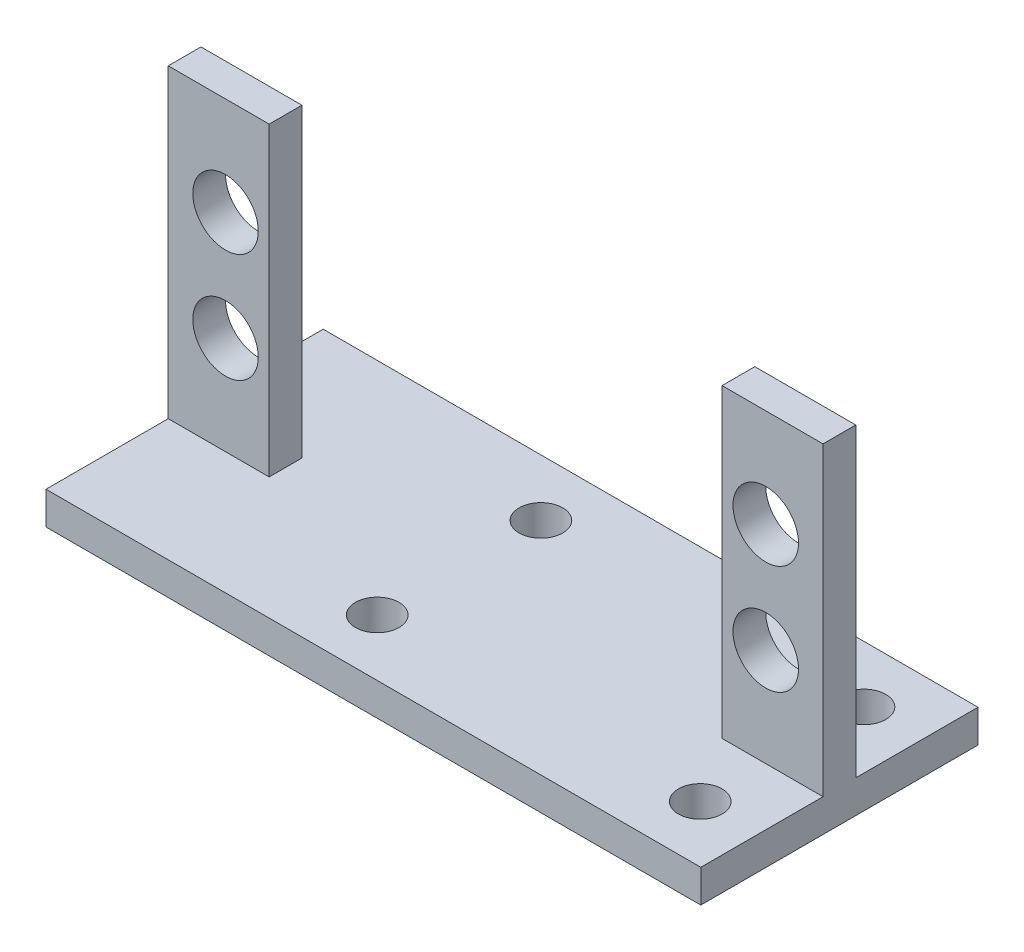
SolidWorks part; units mm, degrees
material "ABS"
ref_plane "Front" through (0, 0, 0) normal (0, 0, 1) x (1, 0, 0)
ref_plane "Top" through (0, 0, 0) normal (0, 1, 0) x (1, 0, 0)
ref_plane "Right" through (0, 0, 0) normal (1, 0, 0) x (0, 0, -1)
sketch "草图1" plane through (0, 0, 0) normal (0, 1, 0) x (1, 0, 0)
  line L0 (0, 0) -> (0, 12.7) construction
  line L1 (0, 0) -> (0, -12.7) construction
  line L2 (0, 0) -> (29, 0) construction
  line L3 (-29, 12.7) -> (29, 12.7)
  line L4 (29, 12.7) -> (29, -12.7)
  line L5 (-29, 12.7) -> (-29, -12.7)
  line L6 (-29, -12.7) -> (29, -12.7)
  point P10 (-29, 0)
extrude "凸台-拉伸1" add sketch "草图1" along normal blind 3
sketch "草图2" plane through (0, 3, 0) normal (0, 1, 0) x (1, 0, 0)
  line L0 (0, 12.7) -> (24.75, 12.7) construction
  line L1 (29, 12.7) -> (-29, 12.7) construction
  line L2 (0, 12.7) -> (-24.75, 12.7) construction
  line L3 (-24.75, 12.7) -> (-24.75, 9.7) construction
  line L4 (-24.75, 9.7) -> (-28.75, 9.7) construction
  line L5 (-24.75, 9.7) -> (-20.75, 9.7) construction
  line L6 (24.75, 12.7) -> (24.75, 9.7) construction
  line L7 (24.75, 9.7) -> (28.75, 9.7) construction
  line L8 (24.75, 9.7) -> (20.75, 9.7) construction
  line L9 (-20.75, 9.7) -> (-28.75, 9.7)
  line L10 (-28.75, 9.7) -> (-28.75, 12.7)
  line L11 (-28.75, 12.7) -> (-20.75, 12.7)
  line L12 (-20.75, 12.7) -> (-20.75, 9.7)
  line L13 (20.75, 9.7) -> (28.75, 9.7)
  line L14 (28.75, 9.7) -> (28.75, 12.7)
  line L15 (28.75, 12.7) -> (20.75, 12.7)
  line L16 (20.75, 12.7) -> (20.75, 9.7)
  line L17 (-20.75, 0) -> (-20.75, 1.5) construction
  line L18 (-20.75, 1.5) -> (-28.75, 1.5) construction
  line L19 (-28.75, 1.5) -> (-28.75, -1.5) construction
  line L20 (-28.75, -1.5) -> (-20.75, -1.5) construction
  line L21 (-20.75, -1.5) -> (-20.75, 0) construction
  line L22 (0, 0) -> (0, 4.2412) construction
  line L23 (-28.75, 1.5) -> (-20.75, 1.5)
  line L24 (-20.75, 1.5) -> (-20.75, -1.5)
  line L25 (-20.75, -1.5) -> (-28.75, -1.5)
  line L26 (-28.75, -1.5) -> (-28.75, 1.5)
  line L27 (28.75, -1.5) -> (28.75, 1.5)
  line L28 (20.75, -1.5) -> (28.75, -1.5)
  line L29 (20.75, 1.5) -> (20.75, -1.5)
  line L30 (28.75, 1.5) -> (20.75, 1.5)
extrude "凸台-拉伸2" add sketch "草图2" along normal blind 28
sketch "草图3" plane through (0, 0, -9.7) normal (0, 0, 1) x (1, 0, 0)
  line L0 (-24.75, 17) -> (-20.75, 17) construction
  line L2 (-24.75, 17) -> (-24.75, 22) construction
  line L3 (-20.75, 31) -> (-20.75, 3) construction
  line L4 (-24.75, 17) -> (-24.75, 12) construction
  line L5 (0, 0) -> (0, 3) construction
  line L6 (-29, 3) -> (29, 3) construction
  circle A0 centre (-24.75, 12) radius 3
  circle A1 centre (-24.75, 22) radius 3
  circle A2 centre (24.75, 12) radius 3
  circle A3 centre (24.75, 22) radius 3
extrude "切除-拉伸1" cut sketch "草图3" against normal mid plane 24
sketch "草图4" plane through (0, 3, 0) normal (0, 1, 0) x (1, 0, 0)
  line L0 (0, 0) -> (24.75, 0) construction
  line L1 (24.75, 0) -> (24.75, 12.7) construction
  line L2 (28.75, 12.7) -> (20.75, 12.7) construction
  line L3 (24.75, 12.7) -> (9.95, 12.7) construction
  line L4 (20.75, 12.7) -> (-20.75, 12.7) construction
  line L5 (9.95, 12.7) -> (9.95, 0) construction
  line L6 (9.95, 0) -> (9.95, -12.7) construction
  line L7 (-29, -12.7) -> (29, -12.7) construction
  line L8 (9.95, 6.35) -> (-4.85, 6.35) construction
  line L9 (24.75, 0) -> (24.75, -7.5) construction
  circle A4 centre (24.75, -7.5) radius 2
  circle A5 centre (24.75, 7.5) radius 2
  circle A6 centre (-4.85, 7.5) radius 2
  circle A7 centre (-4.85, -7.5) radius 2
extrude "切除-拉伸2" cut sketch "草图4" against normal blind 22
sketch "草图8" plane through (0, 31, 0) normal (0, 1, 0) x (1, 0, 0)
  line L0 (-28.75, 12.7) -> (-28.75, 9.7)
  line L1 (-28.75, 9.7) -> (-20.75, 9.7)
  line L2 (-20.75, 9.7) -> (-20.75, 12.7)
  line L3 (-20.75, 12.7) -> (-28.75, 12.7)
  line L4 (20.75, 12.7) -> (20.75, 9.7)
  line L5 (20.75, 9.7) -> (28.75, 9.7)
  line L6 (28.75, 9.7) -> (28.75, 12.7)
  line L7 (28.75, 12.7) -> (20.75, 12.7)
extrude "切除-拉伸3" cut sketch "草图8" against normal blind 28
sketch "草图9" plane through (29, 0, 0) normal (1, 0, 0) x (0, 0, -1)
  line L0 (-12.7, 3) -> (-1.5, 3)
  line L1 (-1.5, 3) -> (-1.5, 31)
  line L2 (-1.5, 31) -> (1.5, 31)
  line L3 (1.5, 31) -> (1.5, 3)
  line L4 (1.5, 3) -> (12.7, 3)
  line L5 (12.7, 3) -> (12.7, 0)
  line L6 (12.7, 0) -> (-12.7, 0)
  line L7 (-12.7, 0) -> (-12.7, 3)
extrude "凸台-拉伸3" add sketch "草图9" along normal mid plane 2
sketch "草图10" plane through (-29, 0, 0) normal (-1, 0, 0) x (0, 0, 1)
  line L0 (-12.7, 3) -> (-1.5, 3)
  line L1 (-1.5, 3) -> (-1.5, 31)
  line L2 (-1.5, 31) -> (1.5, 31)
  line L3 (1.5, 31) -> (1.5, 3)
  line L4 (1.5, 3) -> (12.7, 3)
  line L5 (12.7, 3) -> (12.7, 0)
  line L6 (12.7, 0) -> (-12.7, 0)
  line L7 (-12.7, 0) -> (-12.7, 3)
extrude "凸台-拉伸4" add sketch "草图10" along normal mid plane 2
